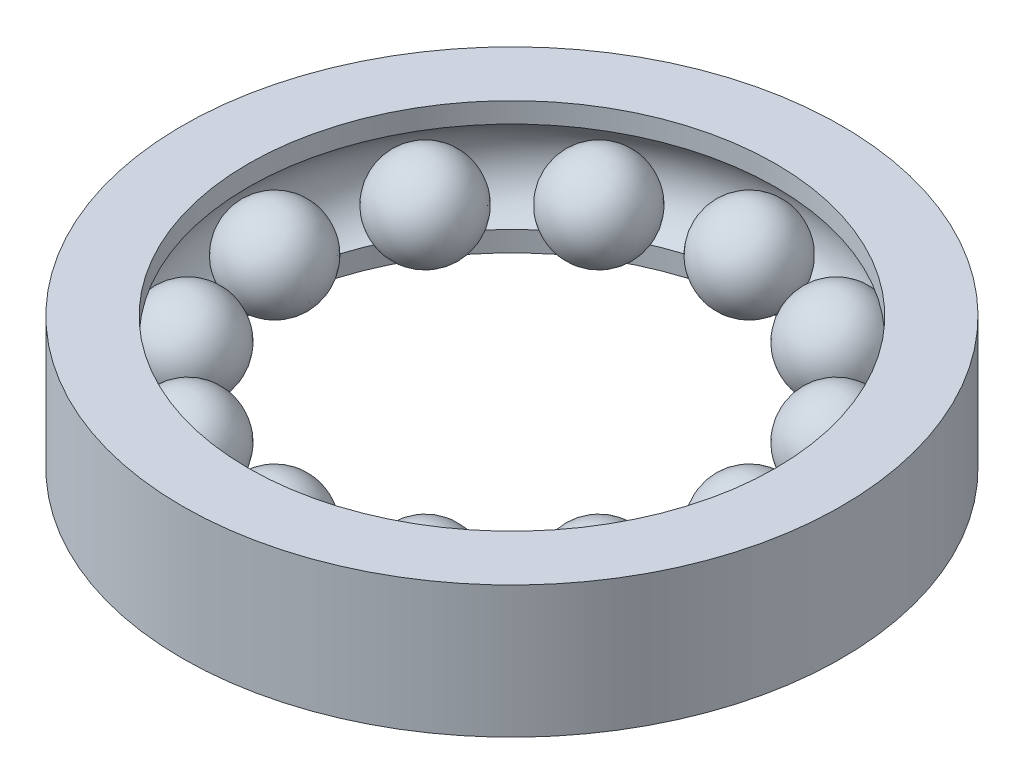
SolidWorks part; units mm, degrees
ref_plane "Ön Düzlem" through (0, 0, 0) normal (0, 0, 1) x (1, 0, 0)
ref_plane "Üst Düzlem" through (0, 0, 0) normal (0, 1, 0) x (1, 0, 0)
ref_plane "Sağ Düzlem" through (0, 0, 0) normal (1, 0, 0) x (0, 0, -1)
sketch "Çizim1" plane through (0, 0, 0) normal (0, 0, 1) x (1, 0, 0)
  line L0 (2, 0.5) -> (2, 0.3464)
  line L1 (2, 0.5) -> (2.5, 0.5)
  line L2 (2, 0.4) -> (2.5, 0.5) construction
  line L3 (2, -0.5) -> (2.5, -0.5)
  line L4 (2.5, 0.5) -> (2.5, -0.5)
  line L5 (0, 0.5) -> (0, -0.5) construction
  line L7 (2, -0.5) -> (2, -0.3464)
  line L9 (2, -0.4) -> (2.5, -0.5) construction
  arc A0 (2, -0.3464) -> (2, 0.3464) centre (1.8, 0) ccw
  point P0 (0, 0)
  dimension "D3" = 0.8
  dimension "D1" = 2.5
  dimension "D2" = 1
  dimension "D4" = 1.8
  dimension "D5" = 0.5
revolve "Döndür1" add sketch "Çizim1" angle 360 about L5
sketch "Çizim3" plane through (0, 0, 0) normal (0, 1, 0) x (1, 0, 0)
  line L0 (1.8, 0.35) -> (1.8, -0.35)
  arc A0 (1.8, -0.35) -> (1.8, 0.35) centre (1.8, 0) ccw
  dimension "D1" = 0.7
  dimension "D2" = 1.8
revolve "Döndür3" add sketch "Çizim3" angle 360 about L0
sketch "Çizim4" plane through (0, 0, 0) normal (0, 1, 0) x (1, 0, 0)
  line L0 (0, 0) -> (1.7321, 1) construction
  line L1 (0, 0) -> (2, 0) construction
  line L2 (1.5588, 1.25) -> (1.5588, 0.55)
  circle A0 centre (0, 0) radius 2 construction
  arc A1 (1.5588, 0.55) -> (1.5588, 1.25) centre (1.5588, 0.9) ccw
  dimension "D3" = 0.7
  dimension "D1" = 30
  dimension "D2" = 1.8
revolve "Döndür4" add sketch "Çizim4" angle 360 about L2
sketch "Çizim5" plane through (0, 0, 0) normal (0, 1, 0) x (1, 0, 0)
  line L0 (0, 0) -> (2, 0) construction
  line L1 (0, 0) -> (1, 1.7321) construction
  line L2 (0.9, 1.9088) -> (0.9, 1.2088)
  circle A0 centre (0, 0) radius 2 construction
  arc A1 (0.9, 1.2088) -> (0.9, 1.9088) centre (0.9, 1.5588) ccw
  dimension "D3" = 0.7
  dimension "D1" = 60
  dimension "D2" = 1.8
revolve "Döndür5" add sketch "Çizim5" angle 360 about L2
sketch "Çizim6" plane through (0, 0, 0) normal (0, 1, 0) x (1, 0, 0)
  line L0 (0, 0) -> (0, 2) construction
  line L1 (0, 2.15) -> (0, 1.45)
  circle A0 centre (0, 0) radius 2 construction
  arc A1 (0, 1.45) -> (0, 2.15) centre (0, 1.8) ccw
  dimension "D2" = 0.7
  dimension "D1" = 1.8
revolve "Döndür6" add sketch "Çizim6" angle 360 about L0
sketch "Çizim7" plane through (0, 0, 0) normal (0, 1, 0) x (1, 0, 0)
  line L0 (0, 0) -> (0, 2) construction
  line L1 (0, 0) -> (-1, 1.7321) construction
  line L2 (-0.9, 1.9088) -> (-0.9, 1.2088)
  circle A0 centre (0, 0) radius 2 construction
  arc A1 (-0.9, 1.2088) -> (-0.9, 1.9088) centre (-0.9, 1.5588) ccw
  dimension "D3" = 0.7
  dimension "D1" = 30
  dimension "D2" = 1.8
revolve "Döndür7" add sketch "Çizim7" angle 360 about L2
sketch "Çizim8" plane through (0, 0, 0) normal (0, 1, 0) x (1, 0, 0)
  line L0 (0, 0) -> (-1.7321, 1) construction
  line L1 (0, 0) -> (0, 2) construction
  line L2 (-1.5588, 1.25) -> (-1.5588, 0.55)
  circle A0 centre (0, 0) radius 2 construction
  arc A1 (-1.5588, 0.55) -> (-1.5588, 1.25) centre (-1.5588, 0.9) ccw
  dimension "D3" = 0.7
  dimension "D1" = 60
  dimension "D2" = 1.8
revolve "Döndür8" add sketch "Çizim8" angle 360 about L2
sketch "Çizim9" plane through (0, 0, 0) normal (0, 1, 0) x (1, 0, 0)
  line L0 (-1.8, 0.35) -> (-1.8, -0.35)
  arc A0 (-1.8, -0.35) -> (-1.8, 0.35) centre (-1.8, 0) ccw
  dimension "D2" = 0.7
  dimension "D1" = 1.8
revolve "Döndür9" add sketch "Çizim9" angle 360 about L0
sketch "Çizim10" plane through (0, 0, 0) normal (0, 1, 0) x (1, 0, 0)
  line L0 (0, 0) -> (-2, 0) construction
  line L1 (0, 0) -> (-1.7321, -1) construction
  line L2 (-1.5588, -0.55) -> (-1.5588, -1.25)
  circle A0 centre (0, 0) radius 2 construction
  arc A1 (-1.5588, -1.25) -> (-1.5588, -0.55) centre (-1.5588, -0.9) ccw
  dimension "D2" = 0.7
  dimension "D1" = 30
  dimension "D3" = 1.8
revolve "Döndür10" add sketch "Çizim10" angle 360 about L2
sketch "Çizim11" plane through (0, 0, 0) normal (0, 1, 0) x (1, 0, 0)
  line L0 (0, 0) -> (-1, -1.7321) construction
  line L1 (0, 0) -> (-2, 0) construction
  line L2 (-0.9, -1.2088) -> (-0.9, -1.9088)
  circle A0 centre (0, 0) radius 2 construction
  arc A1 (-0.9, -1.9088) -> (-0.9, -1.2088) centre (-0.9, -1.5588) ccw
  dimension "D3" = 0.7
  dimension "D1" = 60
  dimension "D2" = 1.8
revolve "Döndür11" add sketch "Çizim11" angle 360 about L2
sketch "Çizim12" plane through (0, 0, 0) normal (0, 1, 0) x (1, 0, 0)
  line L0 (0, -1.45) -> (0, -2.15)
  arc A0 (0, -2.15) -> (0, -1.45) centre (0, -1.8) ccw
  dimension "D2" = 0.7
  dimension "D1" = 1.8
revolve "Döndür12" add sketch "Çizim12" angle 360 about L0
sketch "Çizim13" plane through (0, 0, 0) normal (0, 1, 0) x (1, 0, 0)
  line L0 (0, 0) -> (1, -1.7321) construction
  line L1 (0, 0) -> (0, -2) construction
  line L2 (0.9, -1.2088) -> (0.9, -1.9088)
  circle A0 centre (0, 0) radius 2 construction
  arc A1 (0.9, -1.9088) -> (0.9, -1.2088) centre (0.9, -1.5588) ccw
  dimension "D2" = 0.7
  dimension "D1" = 30
  dimension "D3" = 1.8
revolve "Döndür13" add sketch "Çizim13" angle 360 about L2
sketch "Çizim14" plane through (0, 0, 0) normal (0, 1, 0) x (1, 0, 0)
  line L0 (0, 0) -> (1.7321, -1) construction
  line L1 (0, 0) -> (0, -2) construction
  line L2 (1.5588, -0.55) -> (1.5588, -1.25)
  circle A0 centre (0, 0) radius 2 construction
  arc A1 (1.5588, -1.25) -> (1.5588, -0.55) centre (1.5588, -0.9) ccw
  dimension "D3" = 0.7
  dimension "D1" = 60
  dimension "D2" = 1.8
revolve "Döndür14" add sketch "Çizim14" angle 360 about L2
